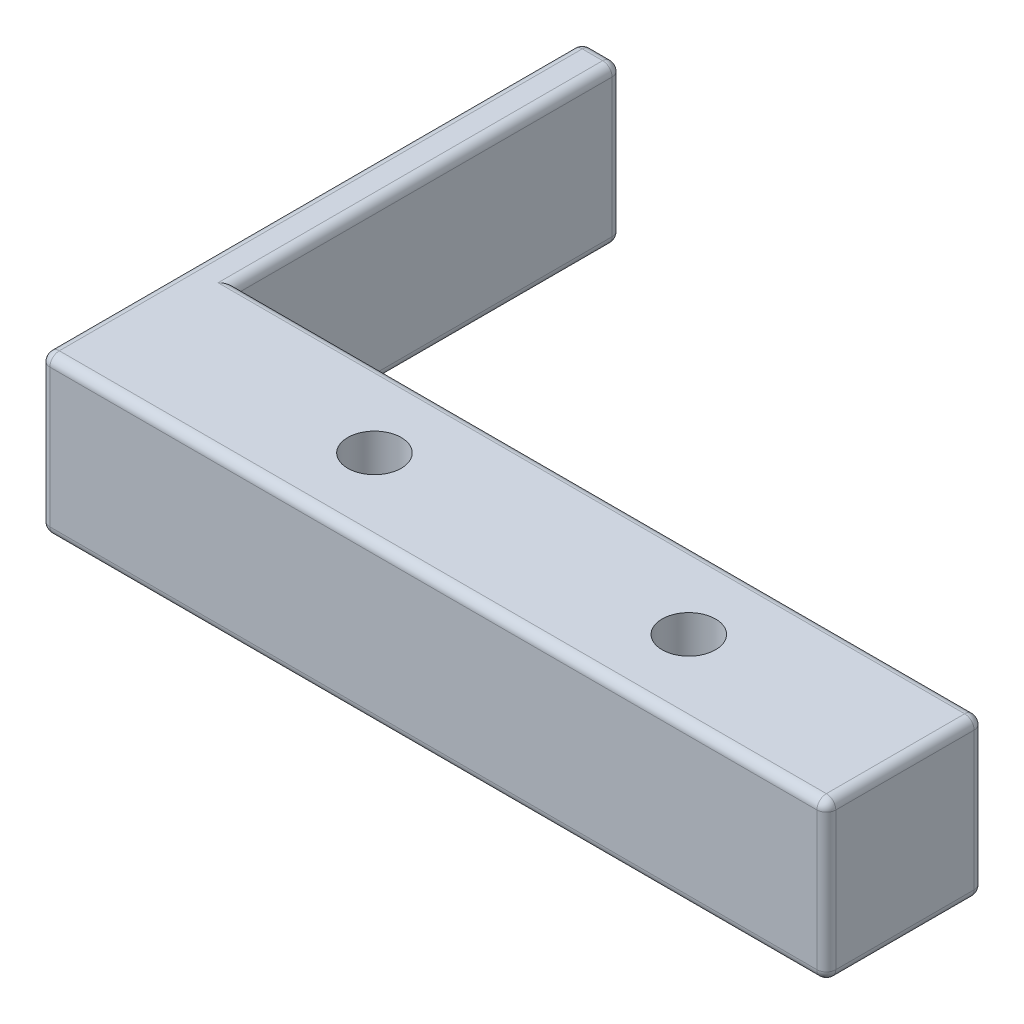
SolidWorks part; units mm, degrees
ref_plane "Front Plane" through (0, 0, 0) normal (0, 0, 1) x (1, 0, 0)
ref_plane "Top Plane" through (0, 0, 0) normal (0, 1, 0) x (1, 0, 0)
ref_plane "Right Plane" through (0, 0, 0) normal (1, 0, 0) x (0, 0, -1)
sketch "Sketch1" plane through (0, 0, 0) normal (0, 1, 0) x (1, 0, 0)
  line L0 (30.1625, 12.7) -> (30.1625, 0) construction
  line L1 (0, 12.7) -> (60.325, 12.7)
  line L2 (0, 12.7) -> (0, 0)
  line L3 (0, 0) -> (60.325, 0)
  line L4 (60.325, 12.7) -> (60.325, 0)
  line L5 (17.4625, 6.35) -> (42.8625, 6.35) construction
  circle A0 centre (17.4625, 6.35) radius 2.159
  circle A1 centre (42.8625, 6.35) radius 2.159
  point P9 (30.1625, 6.35)
  dimension "D3" = 4.318
  dimension "D1" = 12.7
  dimension "D2" = 60.325
  dimension "D4" = 25.4
extrude "Boss-Extrude1" add sketch "Sketch1" along normal blind 12.7
sketch "Sketch4" plane through (0, 0, 0) normal (-1, 0, 0) x (0, 0, 1)
  line L0 (-12.7, 0) -> (0, 0) construction
  line L1 (-43.7753, 12.7) -> (0, 12.7)
  line L2 (-43.7753, 12.7) -> (-43.7753, 0)
  line L3 (-43.7753, 0) -> (0, 0)
  line L4 (0, 12.7) -> (0, 0)
  line L5 (0, 12.7) -> (0, 0) construction
  line L6 (-12.7, 12.7) -> (0, 12.7) construction
extrude "Boss-Extrude2" add sketch "Sketch4" along normal blind 3.175
sketch "Sketch5" plane through (0, 0, 0) normal (0, -1, 0) x (1, 0, 0)
  circle A0 centre (42.8625, -6.35) radius 3.556
  circle A1 centre (17.4625, -6.35) radius 3.556
  circle A2 centre (42.8625, -6.35) radius 2.159 construction
  circle A3 centre (17.4625, -6.35) radius 2.159 construction
  dimension "D1" = 7.112
extrude "Cut-Extrude1" cut sketch "Sketch5" against normal blind 3.81
fillet "Fillet5" radius 0.762 19 edges at (-3.175, 6.35, -43.7753) (-3.175, 0, -21.8876) (60.325, 0, -6.35) (28.575, 0, 0) (-3.175, 12.7, -21.8876) (28.575, 12.7, 0) (60.325, 12.7, -6.35) (30.1625, 12.7, -12.7) (0, 12.7, -28.2376) (0, 0, -28.2376) (30.1625, 0, -12.7) (-3.175, 6.35, 0) (60.325, 6.35, 0) (60.325, 6.35, -12.7) (0, 6.35, -43.7753) (-1.5875, 0, -43.7753) (-1.5875, 12.7, -43.7753) (17.4625, 0, -9.906) (42.8625, 0, -9.906)
